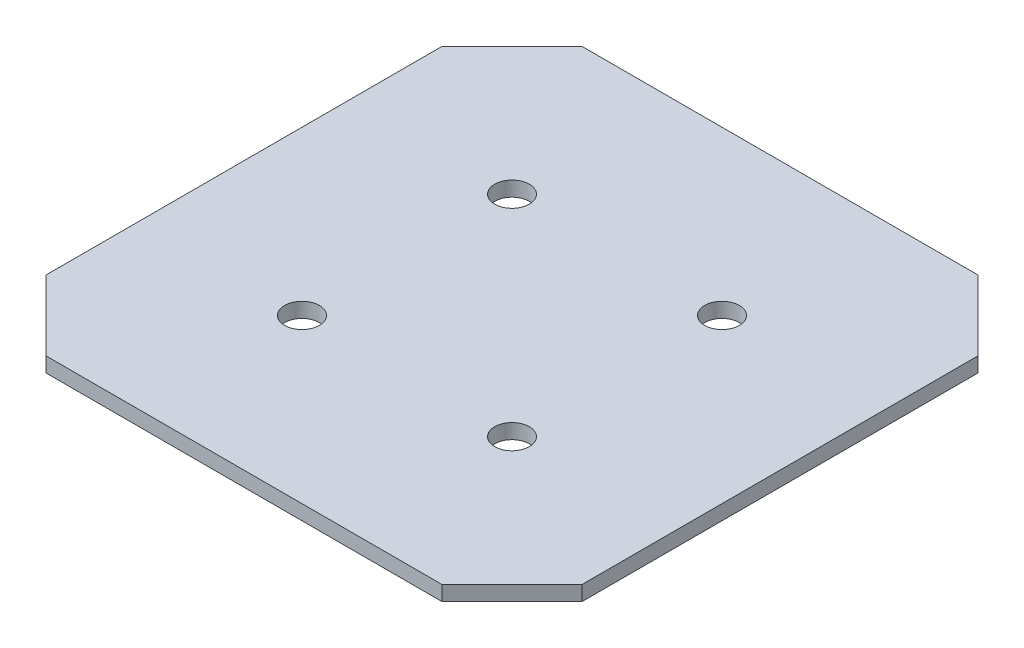
SolidWorks part; units mm, degrees
ref_plane "Front Plane" through (0, 0, 0) normal (0, 0, 1) x (1, 0, 0)
ref_plane "Top Plane" through (0, 0, 0) normal (0, 1, 0) x (1, 0, 0)
ref_plane "Right Plane" through (0, 0, 0) normal (1, 0, 0) x (0, 0, -1)
sketch "Sketch1" plane through (0, 0, 0) normal (0, 1, 0) x (1, 0, 0)
  line L0 (-54.1421, 40) -> (-40, 54.1421)
  line L1 (-40, 54.1421) -> (40, 54.1421)
  line L2 (-54.1421, 40) -> (-54.1421, -40)
  line L3 (-40, -54.1421) -> (40, -54.1421)
  line L4 (54.1421, 40) -> (54.1421, -40)
  line L5 (-54.1421, 54.1421) -> (54.1421, -54.1421) construction
  line L6 (-54.1421, -54.1421) -> (54.1421, 54.1421) construction
  line L7 (40, 54.1421) -> (54.1421, 40)
  line L8 (40, -54.1421) -> (54.1421, -40)
  line L9 (-54.1421, -40) -> (-40, -54.1421)
  line L10 (-54.1421, 54.1421) -> (-40, 54.1421) construction
  line L11 (-54.1421, 54.1421) -> (-54.1421, 40) construction
  line L12 (40, 54.1421) -> (54.1421, 54.1421) construction
  line L13 (54.1421, 54.1421) -> (54.1421, 40) construction
  line L14 (54.1421, -40) -> (54.1421, -54.1421) construction
  line L15 (54.1421, -54.1421) -> (40, -54.1421) construction
  line L16 (-54.1421, -40) -> (-54.1421, -54.1421) construction
  line L17 (-54.1421, -54.1421) -> (-40, -54.1421) construction
  circle A0 centre (-21.2132, 21.2132) radius 3.5
  circle A1 centre (21.2132, 21.2132) radius 3.5
  circle A2 centre (21.2132, -21.2132) radius 3.5
  circle A3 centre (-21.2132, -21.2132) radius 3.5
  point P0 (0, 0)
  point P22 (0, 0)
  point P23 (0, 0)
  dimension "D11" = 7
  dimension "D12" = 7
  dimension "D13" = 7
  dimension "D14" = 7
  dimension "D1" = 80
  dimension "D2" = 20
  dimension "D3" = 90
  dimension "D4" = 90
  dimension "D5" = 90
  dimension "D6" = 90
  dimension "D7" = 20
  dimension "D8" = 20
  dimension "D9" = 20
  dimension "D10" = 80
  dimension "D15" = 30
  dimension "D16" = 30
  dimension "D17" = 30
  dimension "D18" = 30
extrude "Boss-Extrude1" add sketch "Sketch1" along normal blind 3
